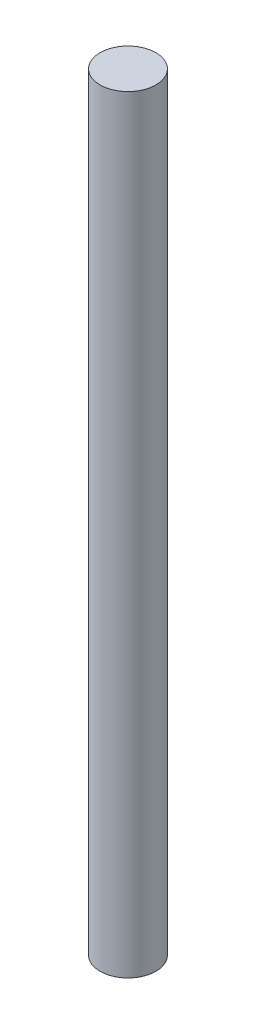
SolidWorks part; units mm, degrees
material "AISI 1045 Aço, trefilado"
ref_plane "Plano frontal" through (0, 0, 0) normal (0, 0, 1) x (1, 0, 0)
ref_plane "Plano superior" through (0, 0, 0) normal (0, 1, 0) x (1, 0, 0)
ref_plane "Plano direito" through (0, 0, 0) normal (1, 0, 0) x (0, 0, -1)
sketch "Esboço1" plane through (0, 0, 0) normal (0, 1, 0) x (1, 0, 0)
  circle A0 centre (0, 0) radius 4
  dimension "D1" = 8
extrude "Ressalto-extrusão1" add sketch "Esboço1" along normal blind 110
